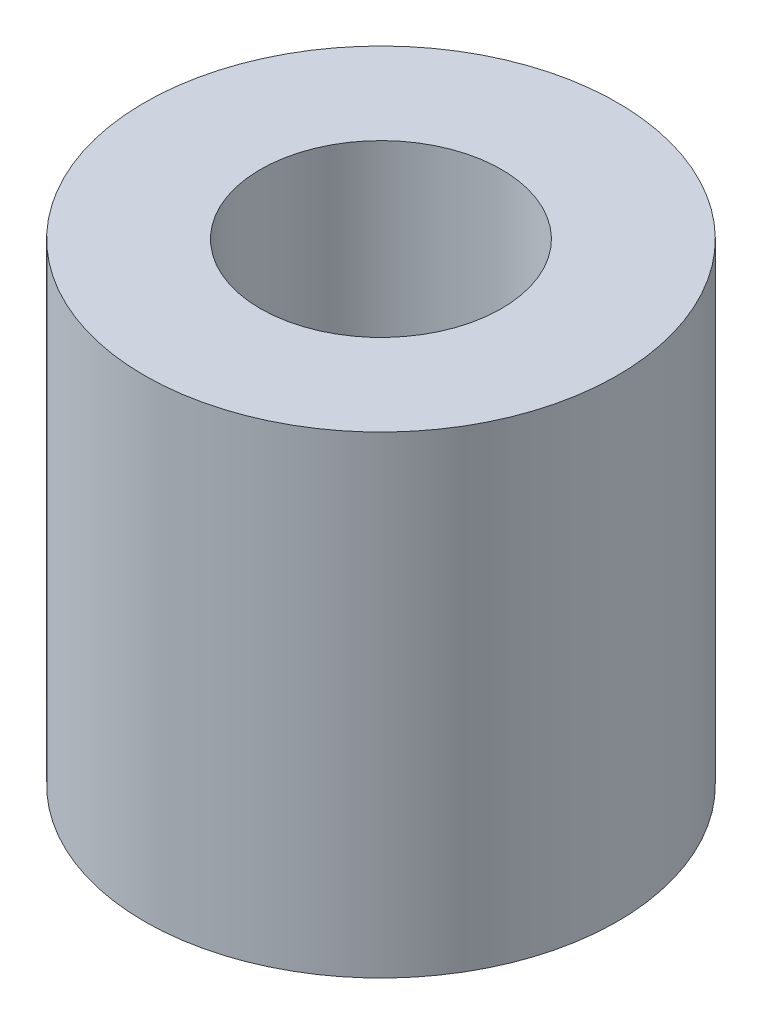
SolidWorks part; units mm, degrees
ref_plane "Front Plane" through (0, 0, 0) normal (0, 0, 1) x (1, 0, 0)
ref_plane "Top Plane" through (0, 0, 0) normal (0, 1, 0) x (1, 0, 0)
ref_plane "Right Plane" through (0, 0, 0) normal (1, 0, 0) x (0, 0, -1)
sketch "Sketch1" plane through (0, 0, 0) normal (0, 1, 0) x (1, 0, 0)
  circle A0 centre (0, 0) radius 2.55
  circle A1 centre (0, 0) radius 5
  dimension "D1" = 5.1
  dimension "D2" = 10
extrude "Boss-Extrude1" add sketch "Sketch1" along normal blind 10
